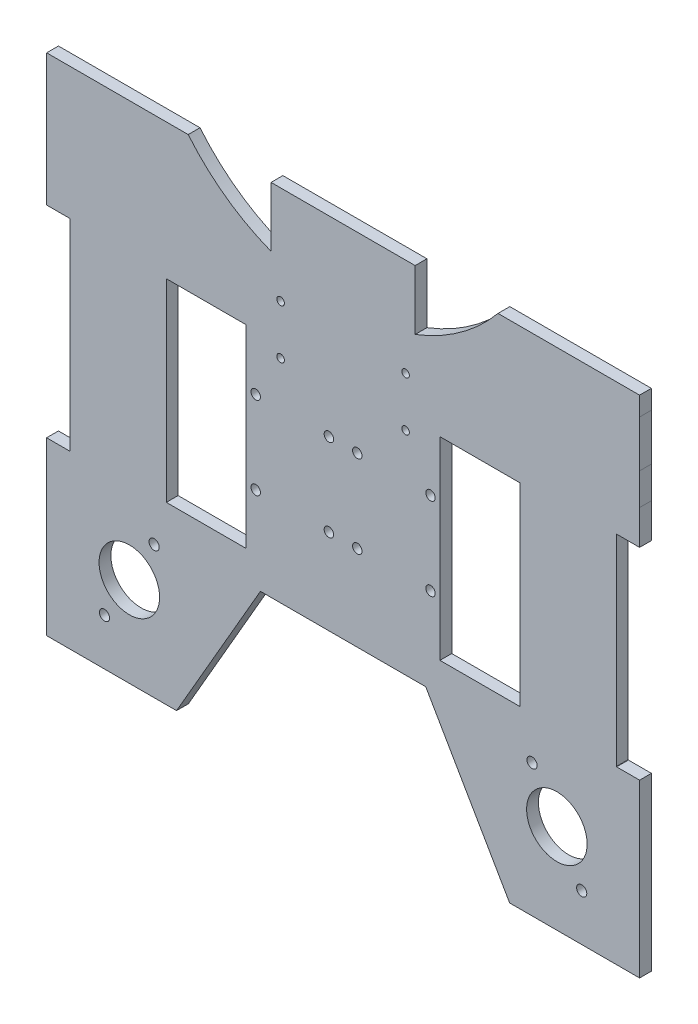
SolidWorks part; units mm, degrees
ref_plane "Front Plane" through (0, 0, 0) normal (0, 0, 1) x (1, 0, 0)
ref_plane "Top Plane" through (0, 0, 0) normal (0, 1, 0) x (1, 0, 0)
ref_plane "Right Plane" through (0, 0, 0) normal (1, 0, 0) x (0, 0, -1)
sketch "Sketch1" plane through (0, 0, 0) normal (0, 0, 1) x (1, 0, 0)
  line L0 (74.8539, -28.2234) -> (41.0158, -28.2234)
  line L1 (41.0158, -28.2234) -> (41.0158, 53.8082)
  line L2 (74.8539, 53.8082) -> (74.8539, -28.2234)
  line L3 (41.0158, 53.8082) -> (74.8539, 53.8082)
  line L4 (-74.8539, -28.2234) -> (-74.8539, 53.8082)
  line L5 (-41.0158, -28.2234) -> (-74.8539, -28.2234)
  line L6 (-41.0158, 53.8082) -> (-41.0158, -28.2234)
  line L7 (-74.8539, 53.8082) -> (-41.0158, 53.8082)
  line L36 (125.5323, 103.2626) -> (91.3819, 103.2626)
  line L37 (77.9135, 103.2626) -> (36.2533, 103.2626)
  line L38 (-36.2533, 103.2626) -> (-77.9135, 103.2626)
  line L39 (-91.3819, 103.2626) -> (-125.5323, 103.2626)
  line L40 (-125.5323, 103.2626) -> (-125.5491, 83.5208)
  line L41 (-125.5542, 70.0872) -> (-125.5545, 55.4659)
  line L42 (-125.5545, 55.4659) -> (-115.8389, 55.4659)
  line L43 (-115.7119, 55.3389) -> (-115.7119, -29.7542)
  line L44 (-115.8389, -29.8811) -> (-125.5557, -29.8811)
  line L45 (-125.5557, -29.8811) -> (-125.5557, -59.4245)
  line L46 (-125.5557, -72.8928) -> (-125.5557, -102.4376)
  line L47 (-125.5557, -102.4376) -> (-101.1987, -102.4376)
  line L48 (-87.7304, -102.4376) -> (-70.5228, -102.4376)
  line L49 (-70.5228, -102.4376) -> (-52.5133, -71.2443)
  line L50 (-47.9273, -63.3011) -> (-35.002, -40.9139)
  line L51 (-35.002, -40.9139) -> (-5.3253, -40.9139)
  line L52 (5.3248, -40.9139) -> (35.002, -40.9139)
  line L53 (35.002, -40.9139) -> (47.9273, -63.3011)
  line L54 (52.5133, -71.2443) -> (70.5228, -102.4376)
  line L55 (70.5228, -102.4376) -> (87.7304, -102.4376)
  line L56 (101.1987, -102.4376) -> (125.5557, -102.4376)
  line L57 (125.5557, -102.4376) -> (125.5557, -72.8921)
  line L58 (125.5557, -59.4237) -> (125.5557, -29.8811)
  line L59 (125.5557, -29.8811) -> (115.8389, -29.8811)
  line L60 (115.7119, -29.7542) -> (115.7119, 55.3389)
  line L61 (115.8389, 55.4659) -> (125.5545, 55.4659)
  line L62 (125.5545, 55.4659) -> (125.5542, 70.0771)
  line L63 (125.549, 83.5309) -> (125.5323, 103.2626)
  line L64 (-88.0221, -60.1266) -> (-98.5324, -78.331) construction
  line L65 (0, -8.3425) -> (0, -82.6611) construction
  line L66 (-91.3819, 103.2626) -> (-77.9135, 103.2626)
  line L67 (-125.5491, 83.5208) -> (-125.5542, 70.0872)
  line L68 (77.9135, 103.2626) -> (91.3819, 103.2626)
  line L69 (125.549, 83.5309) -> (125.5542, 70.0771)
  line L70 (125.5557, -59.4237) -> (125.5557, -72.8921)
  line L71 (87.7304, -102.4376) -> (101.1987, -102.4376)
  line L72 (52.5133, -71.2443) -> (47.9273, -63.3011)
  line L73 (-5.3253, -40.9139) -> (5.3248, -40.9139)
  line L74 (-125.5557, -72.8928) -> (-125.5557, -59.4245)
  line L75 (-101.1987, -102.4376) -> (-87.7304, -102.4376)
  line L76 (-47.9273, -63.3011) -> (-52.5133, -71.2443)
  line L77 (-115.8389, 55.4659) -> (-115.7119, 55.4659)
  line L78 (-115.7119, 55.4659) -> (-115.7119, 55.3389)
  line L79 (-115.8389, -29.8811) -> (-115.7119, -29.8811)
  line L80 (-115.7119, -29.8811) -> (-115.7119, -29.7542)
  line L81 (88.0221, -60.1266) -> (98.5324, -78.331) construction
  arc A42 (-36.2533, 103.2626) -> (36.2533, 103.2626) centre (0, 165.3592) ccw
  arc A54 (115.7119, -29.7542) -> (115.8389, -29.8811) centre (115.8389, -29.7542) ccw
  arc A55 (115.8389, 55.4659) -> (115.7119, 55.3389) centre (115.8389, 55.3389) ccw
  circle A57 centre (-101.0324, -82.6611) radius 2.1533
  circle A58 centre (-90.5221, -64.4567) radius 12.8174
  circle A59 centre (-80.0118, -46.2523) radius 2.1533
  circle A60 centre (80.0118, -46.2523) radius 2.1533
  circle A61 centre (90.5221, -64.4567) radius 12.8174
  circle A62 centre (101.0324, -82.6611) radius 2.1533
extrude "Boss-Extrude1" add sketch "Sketch1" along normal blind 5
sketch "Sketch5" plane through (0, 0, 5) normal (0, 0, 1) x (1, 0, 0)
  line L0 (0, 73.2924) -> (0, 135.2924) construction
  line L1 (-30, 73.2924) -> (30, 73.2924) construction
  circle A1 centre (0, 135.2924) radius 62
  dimension "D1" = 62
extrude "Cut-Extrude3" cut sketch "Sketch5" against normal blind 5
sketch "Sketch6" plane through (0, 0, 5) normal (0, 0, 1) x (1, 0, 0)
  circle A0 centre (26.4645, 69.7569) radius 1.6
  circle A1 centre (26.4645, 48.8279) radius 1.6
  circle A2 centre (-26.4645, 69.7569) radius 1.6
  circle A3 centre (-26.4645, 48.8279) radius 1.6
  circle A4 centre (-37.0158, 30.2924) radius 2
  circle A5 centre (-37.0158, -4.7076) radius 2
  circle A6 centre (-6.0158, -4.7076) radius 2
  circle A7 centre (-6.0158, 30.2924) radius 2
  circle A8 centre (6.0158, 30.2924) radius 2
  circle A9 centre (6.0158, -4.7076) radius 2
  circle A10 centre (37.0158, 30.2924) radius 2
  circle A11 centre (37.0158, -4.7076) radius 2
extrude "Cut-Extrude4" cut sketch "Sketch6" against normal blind 10
sketch "Sketch8" plane through (0, 0, 0) normal (0, 0, -1) x (-1, 0, 0)
  line L0 (0, 111.2924) -> (0, 173.2924) construction
  line L1 (-30.5, 111.2924) -> (30.5, 111.2924) construction
  line L2 (-125.5323, 103.2626) -> (-125.5323, 111.2924)
  line L5 (125.5323, 103.2626) -> (125.5323, 111.2924)
  line L6 (125.5323, 111.2924) -> (-125.5323, 111.2924)
  line L27 (125.5323, 103.2626) -> (53.0857, 103.2626)
  line L28 (-53.0857, 103.2626) -> (-125.5323, 103.2626)
  line L29 (-125.5323, 103.2626) -> (-125.549, 83.5309)
  line L30 (-125.549, 83.5309) -> (-125.5542, 70.0771)
  line L31 (-125.5542, 70.0771) -> (-125.5545, 55.4659)
  line L32 (-125.5545, 55.4659) -> (-115.8389, 55.4659)
  line L33 (-115.7119, 55.3389) -> (-115.7119, -29.7542)
  line L34 (-115.8389, -29.8811) -> (-125.5557, -29.8811)
  line L35 (-125.5557, -29.8811) -> (-125.5557, -102.4376)
  line L36 (-125.5557, -102.4376) -> (-70.5228, -102.4376)
  line L37 (-70.5228, -102.4376) -> (-35.002, -40.9139)
  line L38 (-35.002, -40.9139) -> (35.002, -40.9139)
  line L39 (35.002, -40.9139) -> (70.5228, -102.4376)
  line L40 (70.5228, -102.4376) -> (125.5557, -102.4376)
  line L41 (125.5557, -102.4376) -> (125.5557, -29.8811)
  line L42 (125.5557, -29.8811) -> (115.7119, -29.8811)
  line L43 (115.7119, -29.8811) -> (115.7119, 55.4659)
  line L44 (115.7119, 55.4659) -> (125.5545, 55.4659)
  line L45 (125.5545, 55.4659) -> (125.5542, 70.0872)
  line L46 (125.5542, 70.0872) -> (125.5491, 83.5208)
  line L47 (125.5491, 83.5208) -> (125.5323, 103.2626)
  line L48 (125.5323, 103.2626) -> (53.0857, 103.2626)
  line L49 (-53.0857, 103.2626) -> (-125.5323, 103.2626)
  arc A4 (-53.0857, 103.2626) -> (53.0857, 103.2626) centre (0, 135.2924) ccw
  arc A5 (-115.7119, 55.3389) -> (-115.8389, 55.4659) centre (-115.8389, 55.3389) ccw
  arc A6 (-115.8389, -29.8811) -> (-115.7119, -29.7542) centre (-115.8389, -29.7542) ccw
  arc A7 (-53.0857, 103.2626) -> (53.0857, 103.2626) centre (0, 135.2924) ccw
  point P21 (0, 111.2924)
  dimension "D1" = 62
  dimension "D3" = 0
extrude "Boss-Extrude2" add sketch "Sketch8" against normal blind 5
sketch "Sketch10" plane through (0, 0, 5) normal (0, 0, 1) x (1, 0, 0)
  line L3 (-65.588, 111.2924) -> (-30.5, 111.2924)
  line L7 (-30.5, 111.2924) -> (-30.5, 81.2924) construction
  line L9 (-125.5323, 111.2924) -> (125.5323, 111.2924) construction
  line L10 (-30.5, 111.2924) -> (-30.5, 86.0197)
  line L11 (30.5, 111.2924) -> (65.588, 111.2924)
  line L12 (30.5, 81.2924) -> (30.5, 111.2924) construction
  line L13 (30.5, 111.2924) -> (30.5, 86.0197)
  arc A2 (36.0158, 88.3666) -> (65.588, 111.2924) centre (0, 165.3592) ccw
  arc A3 (-65.588, 111.2924) -> (-34.3845, 87.6243) centre (0, 165.3592) ccw
  arc A4 (30.5, 86.0197) -> (65.588, 111.2924) centre (0, 165.3592) ccw
  arc A5 (-65.588, 111.2924) -> (-30.5, 86.0197) centre (0, 165.3592) ccw
  line M24 (125.5323, 111.2924) -> (-125.5323, 111.2924)
  dimension "D1" = 170
extrude "Cut-Extrude5" cut sketch "Sketch10" against normal blind 30 contours A3 A5 L10 M24 | L13 A4 A2 M24
